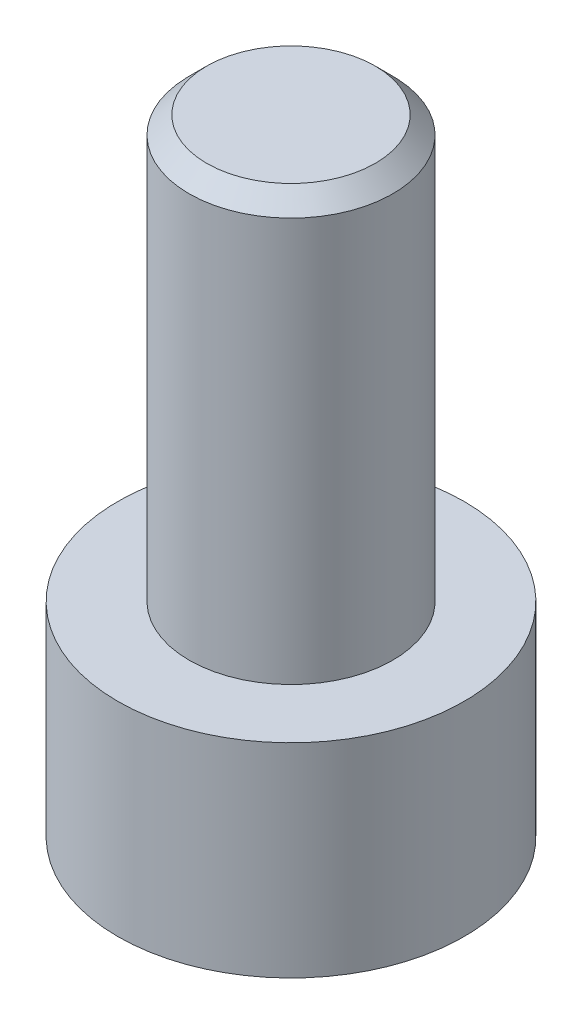
SolidWorks part; units mm, degrees
material "201 Annealed Stainless Steel (SS)"
ref_plane "Front Plane" through (0, 0, 0) normal (0, 0, 1) x (1, 0, 0)
ref_plane "Top Plane" through (0, 0, 0) normal (0, 1, 0) x (1, 0, 0)
ref_plane "Right Plane" through (0, 0, 0) normal (1, 0, 0) x (0, 0, -1)
sketch "Sketch1" plane through (0, 0, 0) normal (0, 1, 0) x (1, 0, 0)
  circle A0 centre (0, 0) radius 2.465
  dimension "D1" = 4.93
extrude "Boss-Extrude1" add sketch "Sketch1" along normal blind 2.9
sketch "Sketch2" plane through (0, 2.9, 0) normal (0, 1, 0) x (1, 0, 0)
  circle A0 centre (0, 0) radius 1.45
  dimension "D1" = 2.9
extrude "Boss-Extrude2" add sketch "Sketch2" along normal blind 6
sketch "Sketch3" plane through (0, 0, 0) normal (0, -1, 0) x (1, 0, 0)
  line L1 (0.7332, -1.27) -> (1.4665, 0)
  line L2 (1.4665, 0) -> (0.7332, 1.27)
  line L3 (0.7332, 1.27) -> (-0.7332, 1.27)
  line L4 (-0.7332, 1.27) -> (-1.4665, 0)
  line L5 (-1.4665, 0) -> (-0.7332, -1.27)
  line L6 (-0.7332, -1.27) -> (0.7332, -1.27)
  circle A0 centre (0, 0) radius 1.27 construction
  dimension "D1" = 2.54
extrude "Cut-Extrude1" cut sketch "Sketch3" against normal blind 1.9
chamfer "Chamfer1" distance 0.25 angle 45 1 edges at (0, 8.9, 1.45)
